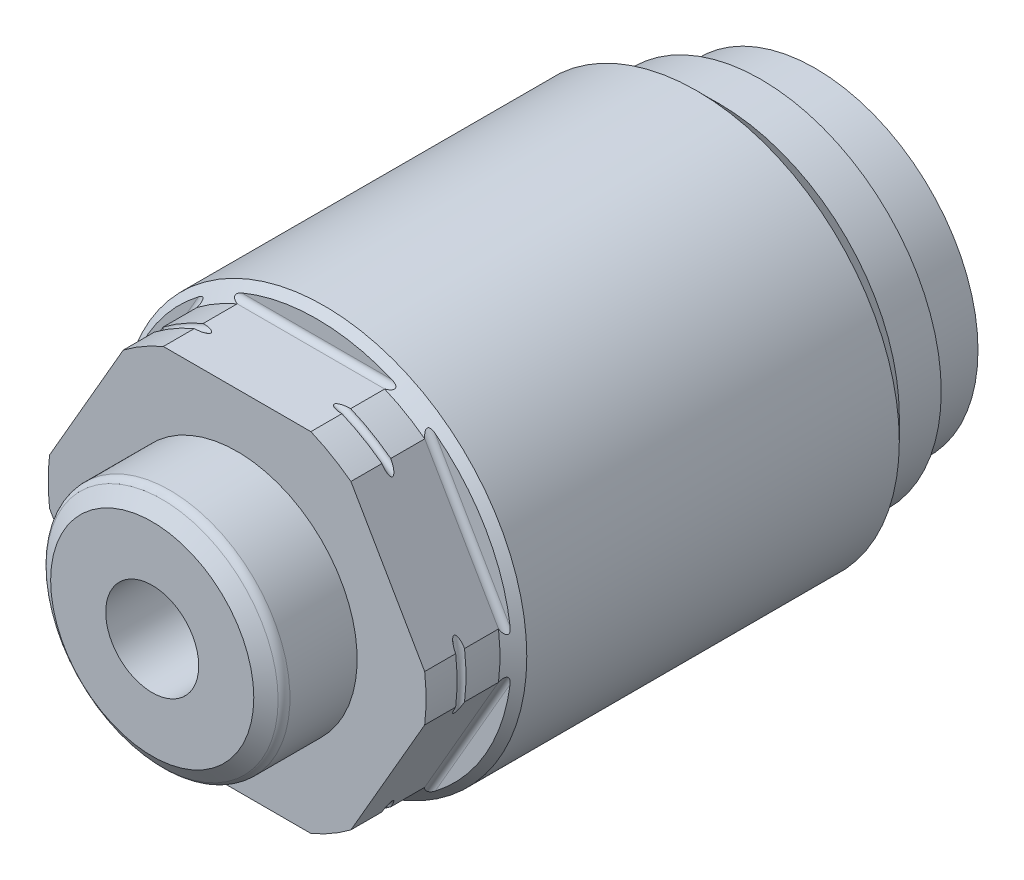
SolidWorks part; units mm, degrees
material "Alloy Steel"
ref_plane "Front Plane" through (0, 0, 0) normal (0, 0, 1) x (1, 0, 0)
ref_plane "Top Plane" through (0, 0, 0) normal (0, 1, 0) x (1, 0, 0)
ref_plane "Right Plane" through (0, 0, 0) normal (1, 0, 0) x (0, 0, -1)
sketch "Sketch1" plane through (0, 0, 0) normal (1, 0, 0) x (0, 0, -1)
  line L0 (0, 0) -> (122.3375, 0) construction
  line L1 (0, 0) -> (0, 13.9954)
  line L2 (0, 13.9954) -> (-4.6736, 13.9954)
  line L3 (-4.6736, 13.9954) -> (-4.6736, 15.5067)
  line L6 (-4.6736, 15.5067) -> (-8.2804, 15.5067)
  line L7 (-8.2804, 15.5067) -> (-10.1854, 17.4117)
  line L8 (-10.1854, 17.4117) -> (-42.2275, 17.4117)
  line L9 (-42.2275, 17.4117) -> (-43.3832, 16.256)
  line L10 (-43.3832, 16.256) -> (-49.7332, 16.256)
  line L11 (-49.7332, 16.256) -> (-49.7332, 0)
  line L12 (0, 0) -> (-49.7332, 0)
  dimension "D1" = 27.9908
  dimension "D2" = 4.6736
  dimension "D5" = 31.0134
  dimension "D6" = 8.2804
  dimension "D7" = 34.8234
  dimension "D8" = 45
  dimension "D9" = 49.7332
  dimension "D10" = 32.512
  dimension "D11" = 45
  dimension "D12" = 6.35
revolve "Revolve1" add sketch "Sketch1" angle 360 about L0
sketch "Sketch2" plane through (0, 0, 0) normal (1, 0, 0) x (0, 0, -1)
  line L0 (0, 0) -> (-47.105, 0) construction
  line L1 (-49.7332, 14.9669) -> (-43.3832, 14.9669)
  line L2 (-49.7332, 16.256) -> (-49.7332, -16.256) construction
  line L3 (-42.8752, 15.4749) -> (-42.8752, 18.1419)
  line L4 (-42.8752, 18.1419) -> (-49.7332, 18.1419)
  line L5 (-49.7332, 18.1419) -> (-49.7332, 14.9669)
  arc A0 (-42.8752, 15.4749) -> (-43.3832, 14.9669) centre (-43.3832, 15.4749) cw
  dimension "D4" = 0.508
  dimension "D1" = 29.9339
  dimension "D2" = 6.858
  dimension "D3" = 3.175
extrude "Cut-Extrude1" cut sketch "Sketch2" against normal through all and the other way through all
pattern_circular "CirPattern1" count 6 over 360 about axis through (0, 0, 0) along (0, 0, 1) of "Cut-Extrude1"
sketch "Sketch3" plane through (0, 0, 0) normal (1, 0, 0) x (0, 0, -1)
  line L0 (0, 0) -> (-60.8041, 0) construction
  line L1 (-57.0357, 0) -> (-57.0357, 8.7376)
  line L2 (-55.5117, 10.3251) -> (-49.7332, 10.3251)
  line L3 (-49.7332, 1.9893) -> (-49.7332, 12.9776) construction
  line L4 (-49.7332, 10.3251) -> (-49.7332, 0)
  line L5 (-49.7332, 1.9893) -> (-49.7332, -1.9893) construction
  line L6 (-49.7332, 0) -> (-57.0357, 0)
  line L7 (0, -13.9954) -> (0, 13.9954) construction
  line L8 (-57.0357, 8.7376) -> (-56.1802, 9.9746)
  arc A0 (-55.5117, 10.3251) -> (-56.1802, 9.9746) centre (-55.5117, 9.5123) ccw
  dimension "D1" = 0.8128
  dimension "D2" = 20.6502
  dimension "D3" = 57.0357
  dimension "D4" = 1.524
  dimension "D5" = 17.4752
revolve "Revolve2" add sketch "Sketch3" angle 360 about L0
sketch "Sketch4" plane through (0, 0, 57.0357) normal (0, 0, 1) x (1, 0, 0)
  circle A0 centre (0, 0) radius 4.0005
  circle A1 centre (0, 0) radius 10.3251 construction
  dimension "D1" = 8.001
extrude "Cut-Extrude2" cut sketch "Sketch4" against normal blind 6.0452
sketch "Sketch5" plane through (0, 0, 0) normal (1, 0, 0) x (0, 0, -1)
  line L0 (-49.7332, 14.9669) -> (-49.7332, 12.9776) construction
  line L1 (0, 0) -> (-52.6213, 0) construction
  line L2 (-47.0662, 19.431) -> (-47.0662, 16.256)
  line L3 (-46.3042, 19.431) -> (-46.3042, 16.256)
  line L4 (-47.0662, 19.431) -> (-46.3042, 19.431)
  arc A0 (-47.0662, 16.256) -> (-46.3042, 16.256) centre (-46.6852, 16.256) ccw
  dimension "D3" = 0.762
  dimension "D1" = 3.048
  dimension "D2" = 16.256
  dimension "D4" = 3.175
revolve "Cut-Revolve1" cut sketch "Sketch5" angle 360 about L1
